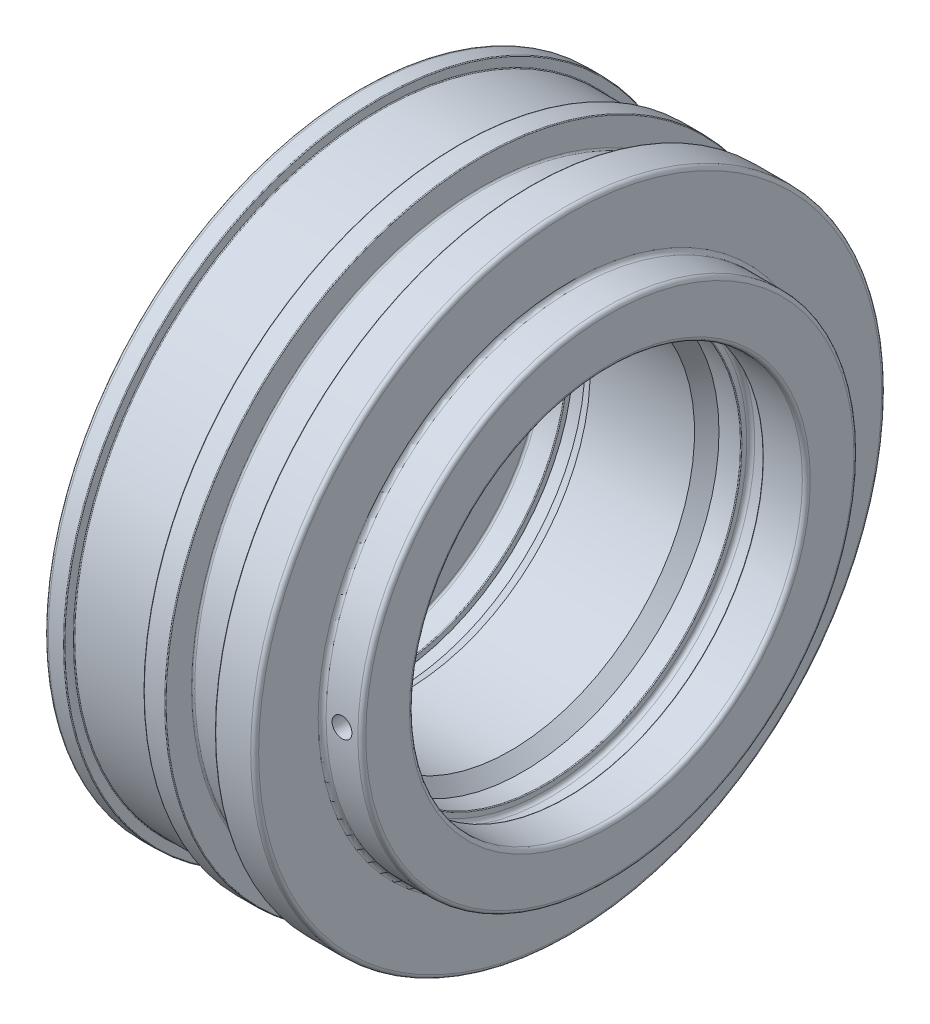
SolidWorks part; units mm, degrees
ref_plane "Front" through (0, 0, 0) normal (0, 0, 1) x (1, 0, 0)
ref_plane "Top" through (0, 0, 0) normal (0, 1, 0) x (1, 0, 0)
ref_plane "Right" through (0, 0, 0) normal (1, 0, 0) x (0, 0, -1)
sketch "Sketch1" plane through (0, 0, 0) normal (0, 0, 1) x (1, 0, 0)
  line L0 (-64.5198, 0) -> (220.5612, 0) construction
  line L1 (15, 67.9142) -> (15, 78.5)
  line L2 (16, 79.5) -> (19.8, 79.5)
  line L3 (58, 79.3) -> (58, 72.9)
  line L4 (57.6, 72.5) -> (45.9, 72.5)
  line L5 (20, 79.3) -> (20, 77.2)
  line L6 (20.2, 77) -> (39.8, 77)
  line L7 (40, 77.2) -> (40, 79.3)
  line L8 (45.5, 72.9) -> (45.5, 79.3)
  line L9 (45.3, 79.5) -> (40.2, 79.5)
  line L10 (58.2, 79.5) -> (67, 79.5)
  line L11 (26.6152, 46.4175) -> (24, 47.75)
  line L12 (52.9175, 46.4175) -> (26.6152, 46.4175)
  line L13 (68, 78.5) -> (68, 63.5)
  line L14 (14.7071, 67.2071) -> (0.2929, 52.7929)
  line L15 (0, 52.0858) -> (0, 0)
  line L16 (52.9175, 46.4175) -> (56, 49.5)
  line L17 (56, 49.5) -> (61.4, 49.5)
  line L18 (24, 47.75) -> (21, 47.75)
  line L19 (21, 47.75) -> (21, 46.45)
  line L20 (69, 62.5) -> (77, 62.5)
  line L21 (78, 61.5) -> (78, 50.5)
  line L22 (61.6, 49.7) -> (61.6, 50.9)
  line L23 (62.6, 51.9) -> (66, 51.9)
  line L24 (67, 50.9) -> (67, 49.7)
  line L25 (20.8, 46.25) -> (15.5, 46.25)
  line L26 (15, 45.75) -> (15, 32.5)
  line L27 (15, 32.5) -> (20, 18.7626)
  line L28 (20, 0) -> (0, 0)
  line L29 (20, 18.7626) -> (20, 0)
  line L30 (67.2, 49.5) -> (77, 49.5)
  arc A0 (45.9, 72.5) -> (45.5, 72.9) centre (45.9, 72.9) cw
  arc A1 (58, 72.9) -> (57.6, 72.5) centre (57.6, 72.9) cw
  arc A2 (20, 77.2) -> (20.2, 77) centre (20.2, 77.2) ccw
  arc A3 (39.8, 77) -> (40, 77.2) centre (39.8, 77.2) ccw
  arc A4 (45.5, 79.3) -> (45.3, 79.5) centre (45.3, 79.3) ccw
  arc A5 (58.2, 79.5) -> (58, 79.3) centre (58.2, 79.3) ccw
  arc A6 (40.2, 79.5) -> (40, 79.3) centre (40.2, 79.3) ccw
  arc A7 (20, 79.3) -> (19.8, 79.5) centre (19.8, 79.3) ccw
  arc A8 (77, 49.5) -> (78, 50.5) centre (77, 50.5) ccw
  arc A9 (15.5, 46.25) -> (15, 45.75) centre (15.5, 45.75) ccw
  arc A10 (77, 62.5) -> (78, 61.5) centre (77, 61.5) cw
  arc A11 (69, 62.5) -> (68, 63.5) centre (69, 63.5) cw
  arc A12 (15, 78.5) -> (16, 79.5) centre (16, 78.5) cw
  arc A13 (67, 79.5) -> (68, 78.5) centre (67, 78.5) cw
  arc A14 (66, 51.9) -> (67, 50.9) centre (66, 50.9) cw
  arc A15 (61.6, 50.9) -> (62.6, 51.9) centre (62.6, 50.9) cw
  arc A16 (67, 49.7) -> (67.2, 49.5) centre (67.2, 49.7) ccw
  arc A17 (61.6, 49.7) -> (61.4, 49.5) centre (61.4, 49.7) cw
  arc A18 (21, 46.45) -> (20.8, 46.25) centre (20.8, 46.45) cw
  arc A19 (14.7071, 67.2071) -> (15, 67.9142) centre (14, 67.9142) ccw
  arc A20 (0.2929, 52.7929) -> (0, 52.0858) centre (1, 52.0858) ccw
  point P67 (67, 49.5)
  point P72 (21, 46.25)
  point P75 (15, 67.5)
  dimension "D15" = 0.2
  dimension "D16" = 145
  dimension "D22" = 22
  dimension "D27" = 0.5
  dimension "D23" = 1
  dimension "D30" = 1
  dimension "D31" = 1
  dimension "D35" = 1
  dimension "D36" = 0.2
  dimension "D38" = 0.2
  dimension "D39" = 1
  dimension "D42" = 0.4
  dimension "D43" = 0.2
  dimension "D1" = 5
  dimension "D3" = 20
  dimension "D4" = 15
  dimension "D5" = 20
  dimension "D6" = 99
  dimension "D7" = 45
  dimension "D8" = 95.5
  dimension "D9" = 92.5
  dimension "D10" = 92.835
  dimension "D11" = 65
  dimension "D12" = 20
  dimension "D13" = 6
  dimension "D14" = 154
  dimension "D17" = 135
  dimension "D18" = 159
  dimension "D19" = 12.5
  dimension "D20" = 10
  dimension "D21" = 45
  dimension "D24" = 27
  dimension "D25" = 53
  dimension "D26" = 3
  dimension "D28" = 78
  dimension "D29" = 125
  dimension "D32" = 5.4
  dimension "D33" = 2.4
  dimension "D34" = 11
  dimension "D37" = 63
  dimension "D40" = 103.8
  dimension "D41" = 30.5
revolve "Base-Revolve" add sketch "Sketch1" angle 360 about L0
cosmetic thread "Cosmetic Thread1" parameters "D2"=95
sketch "Sketch2" plane through (0, 0, 0) normal (0, 0, 1) x (1, 0, 0)
  line L0 (0, 0) -> (78, 0) construction
  line L1 (78, -62.5) -> (78, 62.5) construction
  circle A0 centre (73, 0) radius 2.5
  dimension "D2" = 5
  dimension "D1" = 5
extrude "M6 gevindhul" cut sketch "Sketch2" along normal through all
